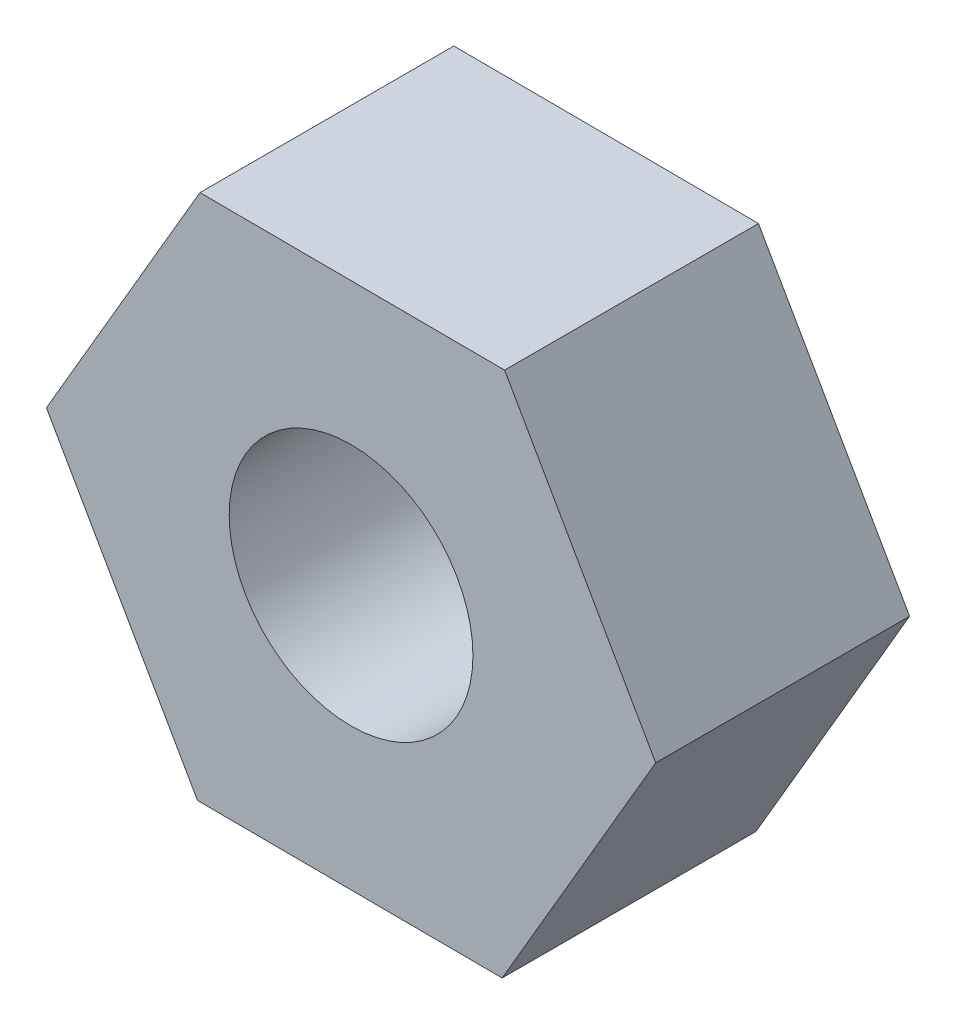
SolidWorks part; units mm, degrees
ref_plane "前视基准面" through (0, 0, 0) normal (0, 0, 1) x (1, 0, 0)
ref_plane "上视基准面" through (0, 0, 0) normal (0, 1, 0) x (1, 0, 0)
ref_plane "右视基准面" through (0, 0, 0) normal (1, 0, 0) x (0, 0, -1)
sketch "草图1" plane through (0, 0, 0) normal (0, 0, 1) x (1, 0, 0)
  line L1 (-2.9757, 5.2102) -> (-6, 0.028)
  line L2 (-6, 0.028) -> (-3.0243, -5.1822)
  line L3 (-3.0243, -5.1822) -> (2.9757, -5.2102)
  line L4 (2.9757, -5.2102) -> (6, -0.028)
  line L5 (6, -0.028) -> (3.0243, 5.1822)
  line L6 (3.0243, 5.1822) -> (-2.9757, 5.2102)
  circle A0 centre (0, 0) radius 5.1962 construction
  circle A1 centre (0, 0) radius 2.4
  dimension "D1" = 4.8
  dimension "D2" = 6
extrude "凸台-拉伸1" add sketch "草图1" along normal blind 5
